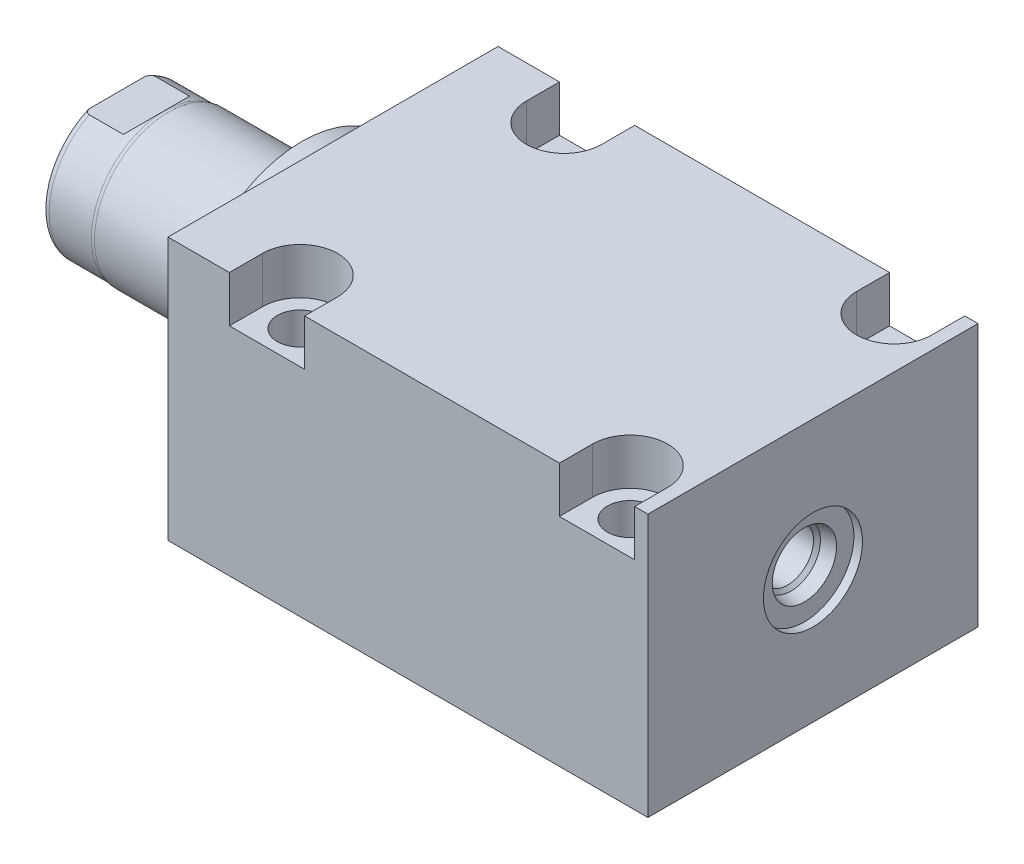
SolidWorks part; units mm, degrees
material "Alloy Steel"
ref_plane "Front Plane" through (0, 0, 0) normal (0, 0, 1) x (1, 0, 0)
ref_plane "Top Plane" through (0, 0, 0) normal (0, 1, 0) x (1, 0, 0)
ref_plane "Right Plane" through (0, 0, 0) normal (1, 0, 0) x (0, 0, -1)
ref_plane "Plane1" through (0, 0, 0) normal (1, 0, 0) x (0, 0, -1)
sketch "Sketch1" plane through (0, 0, 0) normal (1, 0, 0) x (0, 0, -1)
  line L0 (-31.75, 25.146) -> (31.75, 25.146)
  line L1 (31.75, 25.146) -> (31.75, -25.4)
  line L2 (31.75, -25.4) -> (-31.75, -25.4)
  line L3 (-31.75, -25.4) -> (-31.75, 25.146)
  line L4 (0, -24.4475) -> (0, 24.4475) construction
  dimension "D1" = 50.546
  dimension "D2" = 25.4
  dimension "D3" = 63.5
  dimension "D4" = 31.75
extrude "Extrude1" add sketch "Sketch1" along normal blind 92.329
sketch "Sketch5" plane through (0, 0, 0) normal (-1, 0, 0) x (0, 0, 1)
  circle A0 centre (0, 0) radius 22.225
  dimension "D1" = 44.45
extrude "Extrude2" add sketch "Sketch5" along normal blind 5.969
ref_plane "Plane5" through (0, 0, 0) normal (0, -1, 0) x (0, 0, 1)
sketch "Sketch6" plane through (0, 0, 0) normal (0, -1, 0) x (0, 0, 1)
  line L0 (0, 5.969) -> (-14.2875, 5.969)
  line L1 (-14.2875, 5.969) -> (-14.2875, 41.529)
  line L2 (-14.2875, 41.529) -> (0, 41.529)
  line L3 (0, 41.529) -> (0, 5.969)
  line L4 (0, -5.7546) -> (0, 21.1709) construction
  line L5 (22.225, 5.969) -> (-22.225, 5.969) construction
  line L6 (31.75, -92.329) -> (-31.75, -92.329) construction
  dimension "D1" = 133.858
  dimension "D2" = 28.575
revolve "Revolve1" add sketch "Sketch6" angle 360 about L4
ref_plane "Plane6" through (-18.5113, 3.2639, 0) normal (0, 0, 1) x (0, 1, 0)
sketch "S2D0001" plane through (-18.5113, 3.2639, 0) normal (0, 0, 1) x (0, 1, 0)
  line L0 (2.286, 20.95) -> (2.286, 6.6347)
  line L2 (3.4798, 23.0177) -> (-3.2639, 23.0177)
  line L3 (-3.2639, 23.0177) -> (-3.2639, 6.6347)
  line L4 (2.286, 20.95) -> (3.4798, 23.0177)
  line L5 (-3.2639, -18.5113) -> (-3.2639, 2.765) construction
  line L6 (11.0236, 23.0177) -> (-17.5514, 23.0177) construction
  line L7 (2.286, 6.6347) -> (-3.2639, 6.6347)
  dimension "D1" = 30
  dimension "D2" = 13.4874
  dimension "D3" = 11.0998
  dimension "D4" = 16.383
revolve "Cut-Revolve4" cut sketch "S2D0001" angle 360 about L5
ref_plane "Plane7" through (0, 0, 0) normal (0, 1, 0) x (0, 0, -1)
sketch "Sketch8" plane through (0, 0, 0) normal (0, 1, 0) x (0, 0, -1)
  line L0 (-14.2875, 31.623) -> (-14.097, 32.385)
  line L1 (-14.097, 32.385) -> (-14.097, 40.513)
  line L2 (0, 12.6594) -> (0, 20.8178) construction
  line L3 (-14.2875, 31.623) -> (-14.2875, 41.529)
  line L4 (-13.7089, 41.529) -> (-14.2875, 41.529)
  line L5 (14.2875, 41.529) -> (-14.2875, 41.529) construction
  line L6 (-14.2875, 41.529) -> (-14.2875, 5.969) construction
  arc A0 (-13.7089, 41.529) -> (-14.097, 40.513) centre (-12.573, 40.513) ccw
  dimension "D2" = 1.524
  dimension "D1" = 28.194
  dimension "D3" = 1.016
  dimension "D4" = 0.762
  dimension "D5" = 9.144
revolve "Cut-Revolve5" cut sketch "Sketch8" angle 360 about L2
ref_plane "Plane11" through (0, 0, 0) normal (0, 0, -1) x (0, -1, 0)
sketch "Sketch12" plane through (0, 0, 0) normal (0, 0, -1) x (0, -1, 0)
  line L0 (12.573, 41.529) -> (12.573, 33.9598)
  line L1 (12.573, 33.9598) -> (14.097, 32.4358)
  line L2 (-12.573, 41.529) -> (-12.573, 33.9598)
  line L3 (-12.573, 33.9598) -> (-14.097, 32.4358)
  line L4 (12.573, 41.529) -> (14.097, 41.529)
  line L5 (0, 13.7262) -> (0, 20.767) construction
  line L6 (-14.097, 32.4358) -> (-14.097, 41.529)
  line L8 (14.097, 32.385) -> (14.097, 40.513) construction
  line L9 (14.097, 32.4358) -> (14.097, 41.529)
  line L10 (-12.573, 41.529) -> (-14.097, 41.529)
  line L12 (13.7089, 41.529) -> (-13.7089, 41.529) construction
  dimension "D1" = 25.146
  dimension "D2" = 7.5692
  dimension "D3" = 45
extrude "Cut-Extrude4" cut sketch "Sketch12" against normal mid plane 60.96
hole_wizard "Hole2" positions "Sketch17" profile "Sketch16" legacy
sketch "Sketch17" plane through (0, 25.146, 0) normal (0, 1, 0) x (-1, 0, 0)
  line L0 (0, 0) -> (-59.3363, 0) construction
  line L1 (0, -31.75) -> (0, 31.75) construction
  point P0 (-19.05, -25.4)
  point P9 (-19.05, 25.4)
  dimension "D1" = 50.8
  dimension "D2" = 19.05
sketch "Sketch16" plane through (19.05, 25.146, -25.4) normal (1, 0, 0) x (0, 0, 1)
  line L0 (0, 0) -> (0, 50.546)
  line L1 (0, 50.546) -> (4.3688, 50.546)
  line L2 (4.3688, 50.546) -> (4.3688, 0)
  line L3 (4.3688, 0) -> (0, 0)
  line L4 (0, 110) -> (0, -10) construction
  dimension "Diameter" = 8.7376
  dimension "Depth" = 50.546
pattern_linear "LPattern1" count 2 spacing 63.5 along (1, 0, 0) of "Hole2"
sketch "Sketch18" plane through (0, 25.146, 0) normal (0, 1, 0) x (1, 0, 0)
  line L0 (0, 0) -> (50.053, 0) construction
  line L2 (92.329, -31.75) -> (0, -31.75) construction
  line L4 (89.789, -31.75) -> (75.311, -31.75)
  line L5 (11.811, -25.4) -> (11.811, -31.75)
  line L6 (26.289, -25.4) -> (26.289, -31.75)
  line L7 (75.311, -25.4) -> (75.311, -31.75)
  line L8 (89.789, 25.4) -> (89.789, 31.75)
  line L9 (26.289, -31.75) -> (11.811, -31.75)
  line L12 (26.289, 31.75) -> (11.811, 31.75)
  line L14 (75.311, 25.4) -> (75.311, 31.75)
  line L15 (26.289, 25.4) -> (26.289, 31.75)
  line L16 (11.811, 25.4) -> (11.811, 31.75)
  line L17 (89.789, 31.75) -> (75.311, 31.75)
  line L18 (89.789, -25.4) -> (89.789, -31.75)
  arc A0 (26.289, -25.4) -> (11.811, -25.4) centre (19.05, -25.4) ccw
  arc A1 (89.789, -25.4) -> (75.311, -25.4) centre (82.55, -25.4) ccw
  arc A2 (89.789, 25.4) -> (75.311, 25.4) centre (82.55, 25.4) cw
  arc A3 (26.289, 25.4) -> (11.811, 25.4) centre (19.05, 25.4) cw
  dimension "D1" = 14.478
extrude "Cut-Extrude5" cut sketch "Sketch18" against normal blind 8.89
hole_wizard "Hole3" positions "Sketch20" profile "Sketch19" legacy
sketch "Sketch20" plane through (0, -25.4, 0) normal (0, -1, 0) x (1, 0, 0)
  line L0 (0, 31.75) -> (0, -31.75) construction
  point P0 (12.7, 0)
  dimension "D1" = 12.7
sketch "Sketch19" plane through (12.7, -25.4, 0) normal (1, 0, 0) x (0, 0, -1)
  line L0 (0, 0) -> (0, 10.4789)
  line L1 (0, 10.4789) -> (1.5875, 9.525)
  line L2 (1.5875, 9.525) -> (1.5875, 1.4478)
  line L3 (1.5875, 1.4478) -> (5.6705, 1.4478)
  line L4 (5.6705, 0) -> (0, 0)
  line L5 (0, -11.3109) -> (0, 121.1557) construction
  line L6 (0, 10.4789) -> (-1.5875, 9.525) construction
  line L7 (5.6705, 1.4478) -> (5.6705, 0)
  dimension "Depth" = 9.525
  dimension "Drill Angle" = 118
  dimension "Diameter" = 3.175
  dimension "C-Bore Diameter" = 11.3411
  dimension "C-Bore Depth" = 1.4478
hole_wizard "Hole4" positions "Sketch21" profile "Sketch22" legacy
sketch "Sketch21" plane through (0, -25.4, 0) normal (0, -1, 0) x (1, 0, 0)
  point P0 (76.2, 0)
  dimension "D1" = 63.5
sketch "Sketch22" plane through (76.2, -25.4, 0) normal (1, 0, 0) x (0, 0, -1)
  line L0 (0, 0) -> (0, 10.4789)
  line L1 (0, 10.4789) -> (1.5875, 9.525)
  line L2 (1.5875, 9.525) -> (1.5875, 1.4478)
  line L3 (1.5875, 1.4478) -> (5.6705, 1.4478)
  line L4 (5.6705, 0) -> (0, 0)
  line L5 (0, -11.3109) -> (0, 121.1557) construction
  line L6 (0, 10.4789) -> (-1.5875, 9.525) construction
  line L7 (5.6705, 1.4478) -> (5.6705, 0)
  dimension "Depth" = 9.525
  dimension "Drill Angle" = 118
  dimension "Diameter" = 3.175
  dimension "C-Bore Diameter" = 11.3411
  dimension "C-Bore Depth" = 1.4478
chamfer "Chamfer1" distance 0.635 angle 45 2 edges at (76.2, -23.9522, -1.5875) (12.7, -23.9522, -1.5875)
sketch "Sketch23" plane through (0, 0, 0) normal (0, 0, 1) x (1, 0, 0)
  line L0 (12.7, -23.9522) -> (12.7, -21.4272) construction
  line L1 (10.4775, -23.9522) -> (14.9225, -23.9522) construction
  line L2 (7.0294, -23.9522) -> (18.3705, -23.9522) construction
  line L3 (7.0294, -23.9522) -> (7.0294, -25.4) construction
  circle A0 centre (8.4772, -25.4) radius 1.4478
  dimension "D1" = 2.8956
revolve "Revolve2" add sketch "Sketch23" angle 360 about L0
pattern_linear "LPattern3" count 2 spacing 63.5 along (1, 0, 0) of bodies 128
sketch "Sketch24" plane through (0, 0, 0) normal (0, 0, 1) x (1, 0, 0)
  line L0 (0, 0) -> (74.772, 0) construction
  line L1 (92.329, 9.525) -> (90.678, 9.525)
  line L2 (92.329, 25.146) -> (92.329, -25.4) construction
  line L3 (90.678, 9.525) -> (90.678, 6.1849)
  line L4 (90.678, 6.1849) -> (88.1253, 5.6423)
  line L5 (88.1253, 5.6423) -> (87.4614, 4.9784)
  line L6 (87.4614, 4.9784) -> (76.073, 4.9784)
  line L7 (76.073, 4.9784) -> (76.073, 0)
  line L8 (76.073, 0) -> (92.329, 0)
  line L9 (92.329, 0) -> (92.329, 9.525)
  dimension "D1" = 1.651
  dimension "D2" = 19.05
  dimension "D3" = 9.9568
  dimension "D4" = 16.256
  dimension "D5" = 12
  dimension "D6" = 45
  dimension "D7" = 12.3698
  dimension "D8" = 2.5527
revolve "Cut-Revolve6" cut sketch "Sketch24" angle 360 about L0
